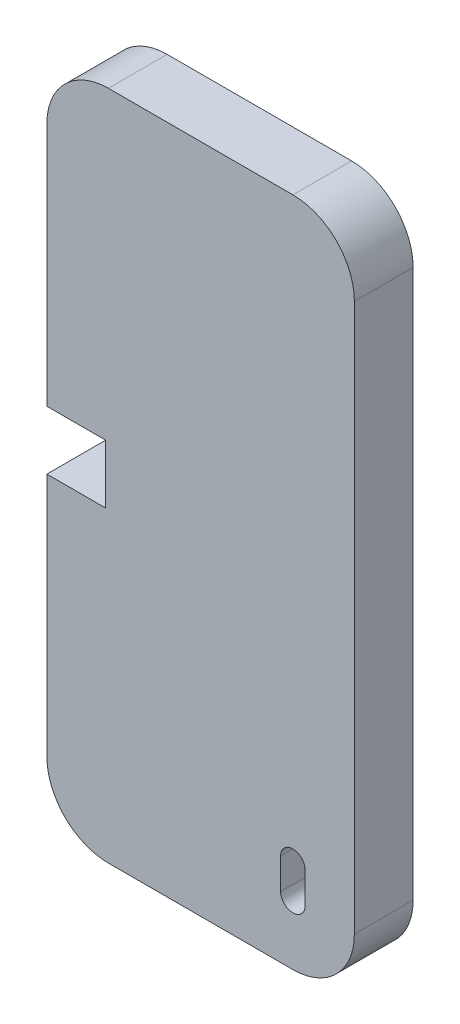
SolidWorks part; units mm, degrees
ref_plane "Front Plane" through (0, 0, 0) normal (0, 0, 1) x (1, 0, 0)
ref_plane "Top Plane" through (0, 0, 0) normal (0, 1, 0) x (1, 0, 0)
ref_plane "Right Plane" through (0, 0, 0) normal (1, 0, 0) x (0, 0, -1)
sketch "Sketch1" plane through (0, 0, 0) normal (0, 0, 1) x (1, 0, 0)
  line L0 (0.2248, 49.7752) -> (7.2248, 49.7752) construction
  line L1 (0.2248, -4.7752) -> (7.2248, -4.7752) construction
  line L2 (0.2248, 49.7752) -> (7.2248, 49.7752) construction
  line L3 (0.2248, -4.7752) -> (7.2248, -4.7752) construction
  line L4 (0.2248, 49.7752) -> (-4.5504, 49.7752) construction
  line L5 (0.2248, -4.7752) -> (-4.5504, -4.7752) construction
  line L6 (-4.5504, 44.7752) -> (-4.5504, 0.2248)
  line L7 (0.4496, -4.7752) -> (15.4496, -4.7752)
  line L8 (0.4496, 49.7752) -> (15.4496, 49.7752)
  line L9 (20.4496, 44.7752) -> (20.4496, 0.2248)
  arc A0 (-4.5504, 44.7752) -> (0.4496, 49.7752) centre (0.4496, 44.7752) cw
  arc A1 (-4.5504, 0.2248) -> (0.4496, -4.7752) centre (0.4496, 0.2248) ccw
  arc A2 (15.4496, -4.7752) -> (20.4496, 0.2248) centre (15.4496, 0.2248) ccw
  arc A3 (15.4496, 49.7752) -> (20.4496, 44.7752) centre (15.4496, 44.7752) cw
  point P16 (20.4496, -4.7752)
  point P19 (20.4496, 49.7752)
  dimension "D5" = 5
  dimension "D1" = 4.7752
  dimension "D2" = 4.7752
  dimension "D3" = 25
  dimension "D4" = 25
extrude "Boss-Extrude1" add sketch "Sketch1" along normal blind 4.7752
sketch "Sketch4" plane through (0, 0, 4.7752) normal (0, 0, 1) x (1, 0, 0)
  line L0 (-4.5504, 44.7752) -> (-4.5504, 22.5)
  line L1 (-4.5504, 44.7752) -> (-4.5504, 0.2248) construction
  line L2 (-4.5504, 22.5) -> (0.2248, 22.5) construction
  line L3 (0.2248, 20.1124) -> (0.2248, 24.8876)
  line L4 (0.2248, 24.8876) -> (-4.5504, 24.8876)
  line L5 (0.2248, 20.1124) -> (-4.5504, 20.1124)
  line L6 (-4.5504, 24.8876) -> (-4.5504, 20.1124)
  arc A0 (0.4496, 49.7752) -> (-4.5504, 44.7752) centre (0.4496, 44.7752) ccw construction
  line M6 (-4.5504, 44.7752) -> (-4.5504, 0.2248)
  dimension "D1" = 4.7752
  dimension "D2" = 2.3876
extrude "Cut-Extrude1" cut sketch "Sketch4" against normal through all contours L0 L2 L3 L4 | L2 L5 L3 M6
sketch "Sketch5" plane through (0, 0, 4.7752) normal (0, 0, 1) x (1, 0, 0)
  line L0 (15.4496, -4.7752) -> (15.4496, 0.2248) construction
  line L2 (15.4496, 0.2248) -> (15.4496, 2.7248)
  line L3 (14.4496, 2.7248) -> (14.4496, 0.2248)
  line L4 (16.4496, 2.7248) -> (16.4496, 0.2248)
  circle A1 centre (15.4496, 2.7248) radius 1
  circle A2 centre (15.4496, 0.2248) radius 1
  point P11 (0, 0)
  point P12 (17.3835, -0.2003)
  point P13 (0, 0)
  dimension "D1" = 2
  dimension "D2" = 2
  dimension "D3" = 2.5
extrude "Cut-Extrude2" cut sketch "Sketch5" against normal blind 10
